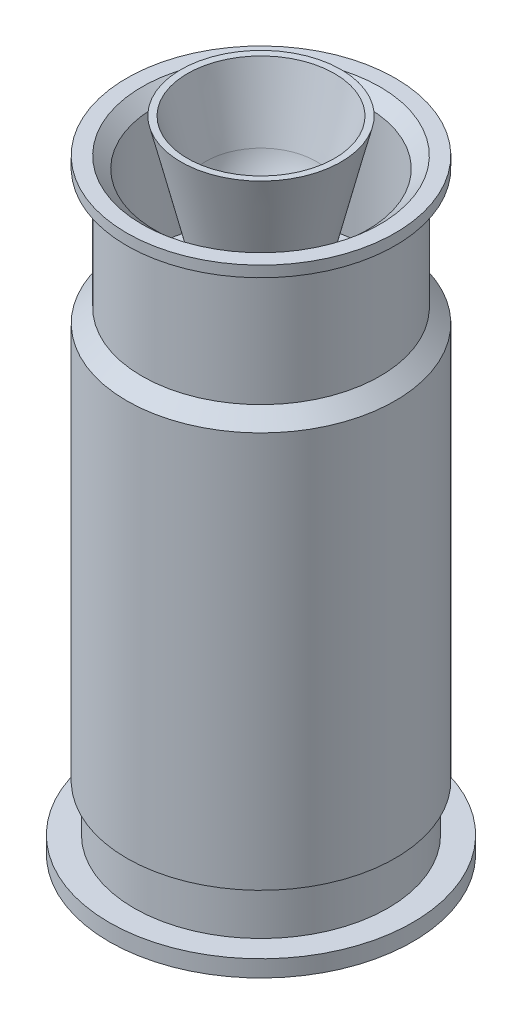
SolidWorks part; units mm, degrees
material "Commercially Pure CP-Ti UNS R50400 (SS)"
ref_plane "Front Plane" through (0, 0, 0) normal (0, 0, 1) x (1, 0, 0)
ref_plane "Top Plane" through (0, 0, 0) normal (0, 1, 0) x (1, 0, 0)
ref_plane "Right Plane" through (0, 0, 0) normal (1, 0, 0) x (0, 0, -1)
sketch "Sketch1" plane through (0, 0, 0) normal (0, 0, 1) x (1, 0, 0)
  line L0 (0, 0) -> (139.7, 0) construction
  line L1 (92.96, 0) -> (92.96, 373.0632) construction
  line L2 (92.96, 10.2) -> (-172.4135, 10.2) construction
  line L3 (77.766, 10.2) -> (77.766, 381.1115) construction
  line L4 (77.766, 38.9) -> (265.2497, 38.9) construction
  line L5 (82.206, 38.9) -> (82.206, 397.7166) construction
  line L6 (82.206, 281.51) -> (-85.1777, 281.51) construction
  line L7 (72.906, 281.51) -> (72.906, 506.1214) construction
  line L8 (72.906, 363.8) -> (286.5207, 363.8) construction
  line L9 (82.206, 370.5) -> (-88.1083, 370.5) construction
  line L10 (72.906, 391.5) -> (-335.5259, 391.5) construction
  line L11 (0, 0) -> (0, 457.2) construction
  line L12 (72.906, 289.93) -> (-182.4311, 289.93) construction
  line L13 (0, 0) -> (92.96, 0)
  line L14 (92.96, 0) -> (92.96, 10.2)
  line L15 (92.96, 10.2) -> (77.766, 10.2)
  line L16 (77.766, 10.2) -> (77.766, 38.9)
  line L17 (77.766, 38.9) -> (82.206, 38.9)
  line L18 (82.206, 38.9) -> (82.206, 281.51)
  line L19 (82.206, 281.51) -> (72.906, 289.93)
  line L20 (72.906, 289.93) -> (72.906, 358.4)
  line L21 (72.906, 358.4) -> (82.206, 363.8)
  line L22 (82.206, 363.8) -> (82.206, 370.5)
  line L23 (24.2982, 289.93) -> (49.045, 391.6229)
  line L24 (82.206, 370.5) -> (72.906, 370.5)
  line L25 (72.906, 370.5) -> (65.0875, 363.5375)
  line L26 (65.0875, 363.5375) -> (65.0875, 230.1875) construction
  line L27 (65.0875, 363.5375) -> (65.0875, 289.93)
  line L28 (65.0875, 289.93) -> (24.2982, 289.93)
  line L29 (8.4074, 289.93) -> (8.4074, 377.2805) construction
  line L30 (33.4074, 289.93) -> (33.4074, 381.1115) construction
  line L31 (33.4074, 304.93) -> (-103.2633, 304.93) construction
  line L32 (33.4074, 304.93) -> (-43.7271, 396.8553) construction
  line L33 (33.4074, 304.93) -> (43.8661, 185.3866) construction
  line L34 (-14.8017, 362.3833) -> (38.7579, 349.3497) construction
  line L35 (0, 4) -> (107.7619, 4) construction
  line L36 (73.766, 10.2) -> (73.766, -35.2723) construction
  line L37 (0, 0) -> (0, 4)
  line L38 (0, 4) -> (73.766, 4)
  line L39 (73.766, 4) -> (73.766, 43.2311)
  line L40 (73.766, 43.2311) -> (77.766, 47.2311)
  line L41 (77.766, 47.2311) -> (77.766, 275.3218)
  line L42 (35.5863, 280.0251) -> (77.766, 275.3218)
  line L43 (33.7805, 350.5609) -> (45.045, 391.5)
  line L44 (45.045, 391.5) -> (49.045, 391.6229)
  line L45 (8.4074, 10.2) -> (67.0787, 10.2)
  line L46 (67.0787, 10.2) -> (73.025, 53.975)
  line L47 (73.025, 53.975) -> (73.025, 273.05)
  line L48 (73.025, 273.05) -> (8.4074, 281.8275)
  line L49 (8.4074, 281.8275) -> (8.4074, 10.2)
  circle A0 centre (33.4074, 304.93) radius 25 construction
  circle A1 centre (39.9441, 230.2154) radius 50 construction
  circle A2 centre (-14.8017, 362.3833) radius 50 construction
  arc A3 (17.3377, 324.0811) -> (33.7805, 350.5609) centre (-14.8017, 362.3833) ccw
  arc A4 (17.3377, 324.0811) -> (35.5863, 280.0251) centre (33.4074, 304.93) ccw
  point P0 (0, 0)
  point P4 (92.96, 0)
  point P7 (92.96, 10.2)
  point P10 (77.766, 10.2)
  point P13 (77.766, 38.9)
  point P16 (82.206, 38.9)
  point P19 (82.206, 281.51)
  point P22 (72.906, 281.51)
  point P25 (72.906, 358.4)
  point P26 (72.906, 289.93)
  point P27 (72.906, 363.8)
  point P30 (82.206, 363.8)
  point P31 (82.206, 370.5)
  point P34 (72.906, 370.5)
  point P35 (72.906, 391.5)
  point P38 (0, 391.5)
  point P39 (49.045, 391.6229)
  point P43 (8.4074, 289.93)
  point P44 (0, 289.93)
  point P45 (24.2982, 289.93)
  point P46 (0, 4)
  point P47 (45.045, 391.5)
  point P52 (65.0875, 363.5375)
  point P53 (65.0875, 289.93)
  point P57 (33.4074, 289.93)
  point P63 (33.4074, 304.93)
  point P66 (8.4074, 304.93)
  point P68 (-14.8017, 362.3833)
  point P71 (39.9441, 230.2154)
  point P76 (73.766, 10.2)
  point P82 (73.766, 4)
  dimension "D1" = 92.96
  dimension "D2" = 10.2
  dimension "D3" = 15.194
  dimension "D4" = 28.7
  dimension "D5" = 4.44
  dimension "D6" = 242.61
  dimension "D7" = 9.3
  dimension "D8" = 8.42
  dimension "D9" = 68.47
  dimension "D10" = 5.4
  dimension "D11" = 6.7
  dimension "D12" = 21
  dimension "D13" = 49.045
  dimension "D14" = 8.4074
  dimension "D15" = 4
  dimension "WHALL_C" = 4
  dimension "D16" = 4
  dimension "D17" = 15
  dimension "R_INTERNAL" = 25
  dimension "D18" = 75
  dimension "D19" = 75
revolve "Revolve1" add sketch "Sketch1" angle 360 about L11
equation "\"D18@Sketch1\" = \"R_INTERNAL\"*3"
equation "\"D19@Sketch1\" = \"R_INTERNAL\"*3"
equation "\"D15@Sketch1\" = \"WHALL_C\""
